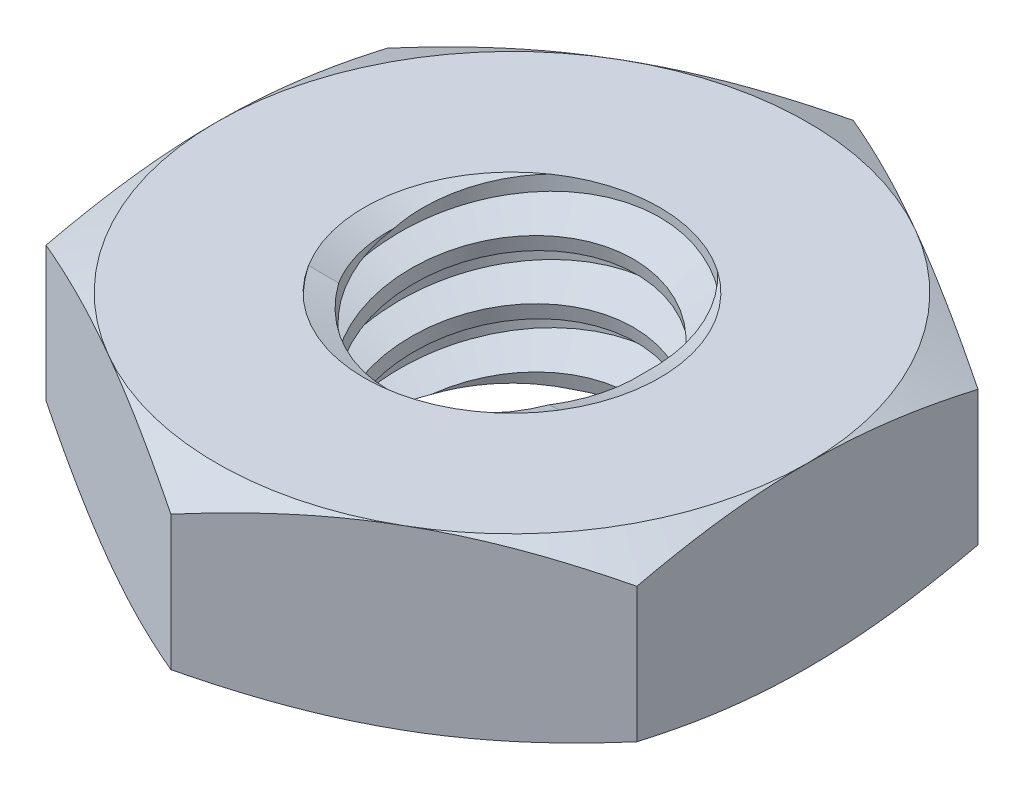
SolidWorks part; units mm, degrees
ref_plane "Front" through (0, 0, 0) normal (0, 0, 1) x (1, 0, 0)
ref_plane "Top" through (0, 0, 0) normal (0, 1, 0) x (1, 0, 0)
ref_plane "Right" through (0, 0, 0) normal (1, 0, 0) x (0, 0, -1)
sketch "Sketch1" plane through (0, 0, 0) normal (0, 1, 0) x (1, 0, 0)
  line L1 (0, 2.3094) -> (-2, 1.1547)
  line L2 (-2, 1.1547) -> (-2, -1.1547)
  line L3 (-2, -1.1547) -> (0, -2.3094)
  line L4 (0, -2.3094) -> (2, -1.1547)
  line L5 (2, -1.1547) -> (2, 1.1547)
  line L6 (2, 1.1547) -> (0, 2.3094)
  circle A0 centre (0, 0) radius 2 construction
  dimension "Hex Flats" = 4
extrude "Extrude1" add sketch "Sketch1" along normal mid plane 1.2
sketch "Sketch2" plane through (0, 0, 0) normal (1, 0, 0) x (0, 0, -1)
  line L0 (-1, -0.6) -> (-1, 0.6) construction
  line L1 (0, -0.6) -> (1, -0.6)
  line L2 (0, -0.6) -> (0, 0.6)
  line L3 (0, 0.6) -> (1, 0.6)
  line L4 (1, -0.6) -> (1, 0.6)
  line L5 (-1.1547, 0.6) -> (1.1547, 0.6) construction
  line L6 (-1.1547, -0.6) -> (1.1547, -0.6) construction
  line L7 (0, -1.6) -> (0, -0.6) construction
  dimension "Thread Dia" = 2
revolve "Revolve1" add sketch "Sketch2" angle 360 about L7
sketch "Sketch3" plane through (0, 0, 0) normal (1, 0, 0) x (0, 0, -1)
  line L0 (1, 0.6) -> (-1, 0.6) construction
  line L1 (-1, 0.6) -> (-1, 0.2) construction
  line L2 (-1, 0.2) -> (1, 0.6) construction
  line L3 (1, 0.6) -> (1.0098, 0.551) construction
  line L4 (1.0098, 0.551) -> (1.0784, 0.2078)
  line L5 (1.0784, 0.2078) -> (0.8416, 0.2879)
  line L6 (0.8416, 0.2879) -> (0.822, 0.3859)
  line L7 (0.822, 0.3859) -> (1.0098, 0.551)
  line L8 (0.8318, 0.3369) -> (1.0441, 0.3794) construction
  line L9 (1, 0.6) -> (1, 0.3705) construction
  line L10 (1, 0.3705) -> (-1, -0.0295) construction
  line L11 (-1, -0.0295) -> (-1, 0.2) construction
  line L12 (-0.0859, 0.6) -> (0.0859, -0.2589) construction
  line L13 (-1, -0.6) -> (-1, 0.6) construction
  line L14 (0, 0.6) -> (1, 0.6) construction
  line L15 (1, -0.6) -> (1, 0.6) construction
  line L16 (0, 0) -> (0, 0.6) construction
  line L17 (-1.0098, 0.551) -> (-1.0784, 0.2078) construction
  line L18 (-0.822, 0.3859) -> (-1.0098, 0.551) construction
  line L19 (-0.8416, 0.2879) -> (-0.822, 0.3859) construction
  line L20 (-1.0784, 0.2078) -> (-0.8416, 0.2879) construction
  line L21 (0.0859, 0.6) -> (-0.0859, -0.2589) construction
  point P13 (0, 0.1705)
  dimension "D1" = 0.05
  dimension "D2" = 0.1
  dimension "Thread Pitch" = 0.4
  dimension "D4" = 60
  dimension "D5" = 0.4
revolve "Cut-Revolve1" cut sketch "Sketch3" angle 360 about L12
pattern_linear "LPattern1" count 3 spacing 0.4 along (0, -1, 0) count 2 spacing 0.4 along (0, 1, 0) of "Cut-Revolve1"
sketch "Sketch4" plane through (0, 0, 0) normal (1, 0, 0) x (0, 0, -1)
  line L0 (0, 0.6) -> (1, 0.6)
  line L1 (1, 0.6) -> (0.822, 0.517)
  line L2 (0.822, 0.517) -> (0.822, -0.517)
  line L3 (0.822, -0.517) -> (1, -0.6)
  line L4 (1, -0.6) -> (0, -0.6)
  line L5 (0, -0.6) -> (0, 0.6)
  line L6 (1, -0.6) -> (1, 0.6) construction
  line L7 (0, 0.6) -> (1, 0.6) construction
  line L8 (0, -0.6) -> (1, -0.6) construction
  line L9 (0, -0.6) -> (0, 0.6) construction
  line L10 (0, 0.6) -> (0, 0.7964) construction
  dimension "D1" = 25
revolve "Cut-Revolve2" cut sketch "Sketch4" angle 360 about L10
combine bodies "Combine1" operation type subtract main body 112 bodies to subtract 111
sketch "Sketch5" plane through (0, 0, 0) normal (1, 0, 0) x (0, 0, -1)
  line L0 (0, -0.6) -> (2, -0.6)
  line L1 (2, -0.6) -> (2.3094, -0.4557)
  line L2 (2.3094, -0.4557) -> (2.3094, 0.4557)
  line L3 (2.3094, 0.4557) -> (2, 0.6)
  line L4 (0, 0.6) -> (0, 1.87)
  line L5 (0, 1.87) -> (3.5794, 1.87)
  line L6 (3.5794, 1.87) -> (3.5794, -1.87)
  line L7 (3.5794, -1.87) -> (0, -1.87)
  line L8 (0, -1.87) -> (0, -0.6)
  line L9 (2, 0.6) -> (2, -0.6) construction
  line L11 (0, -0.6) -> (1, -0.6) construction
  line L12 (2, 0.6) -> (0, 0.6)
  line L13 (2.3094, 0) -> (3.5794, 0) construction
  line L14 (2.3094, 0.6) -> (2.3094, -0.6) construction
  line L15 (0, -0.6) -> (0, 0.6) construction
  line L17 (0, 0) -> (2, 0) construction
  line L22 (0, 0.6) -> (1, 0.6) construction
  dimension "D1" = 25
  dimension "D2" = 1.27
  dimension "D3" = 1.2
revolve "Cut-Revolve3" cut sketch "Sketch5" angle 360 about L15
equation "\"D1@Sketch3\"=\"Thread Pitch@Sketch3\"/8"
equation "\"D2@Sketch3\"=\"Thread Pitch@Sketch3\"/4"
equation "\"D5@Sketch3\"=\"Thread Pitch@Sketch3\""
equation "\"D4@LPattern1\"=\"Thread Pitch@Sketch3\""
equation "\"D3@LPattern1\"=\"Thread Pitch@Sketch3\""
equation "\"D1@LPattern1\"=\"Height@Extrude1\"/\"Thread Pitch@Sketch3\""
